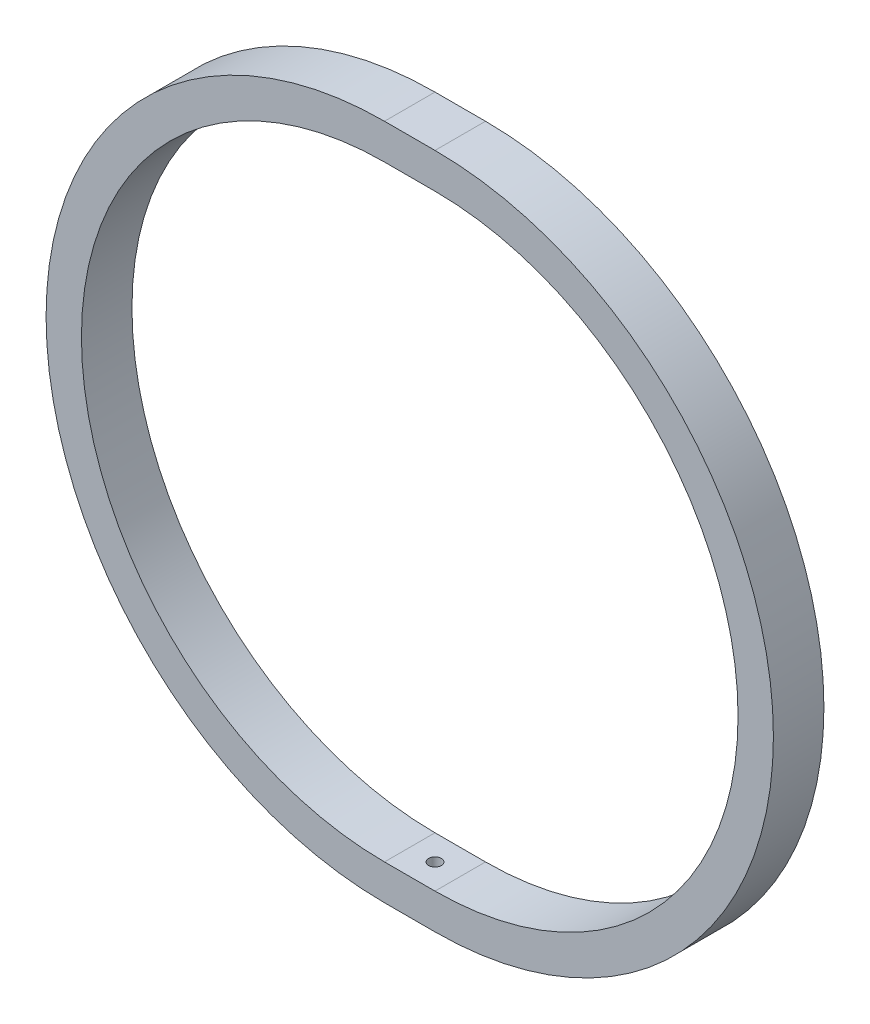
SolidWorks part; units mm, degrees
ref_plane "Front Plane" through (0, 0, 0) normal (0, 0, 1) x (1, 0, 0)
ref_plane "Top Plane" through (0, 0, 0) normal (0, 1, 0) x (1, 0, 0)
ref_plane "Right Plane" through (0, 0, 0) normal (1, 0, 0) x (0, 0, -1)
sketch "Sketch1" plane through (0, 0, 0) normal (1, 0, 0) x (0, 0, -1)
  line L0 (-29.8744, 0) -> (27.9622, 0) construction
  line L1 (-5, 67) -> (5, 67)
  line L2 (-5, 67) -> (-5, 60)
  line L3 (-5, 60) -> (5, 60)
  line L4 (5, 67) -> (5, 60)
  dimension "D1" = 7
  dimension "D2" = 10
  dimension "D3" = 5
  dimension "D4" = 60
revolve "Revolve1" add sketch "Sketch1" angle 180 about L0
sketch "Sketch2" plane through (0, 0, 0) normal (1, 0, 0) x (0, 0, -1)
  line L0 (-5, 67) -> (-5, 60) construction
  line L1 (-5, 60) -> (5, 60) construction
  line L2 (5, 60) -> (5, 67) construction
  line L3 (5, 67) -> (-5, 67) construction
  line L4 (-5, -60) -> (-5, -67) construction
  line L5 (-5, -67) -> (5, -67) construction
  line L6 (5, -67) -> (5, -60) construction
  line L7 (5, -60) -> (-5, -60) construction
  line L8 (-5, 67) -> (-5, 60)
  line L9 (-5, 60) -> (5, 60)
  line L10 (5, 60) -> (5, 67)
  line L11 (5, 67) -> (-5, 67)
  line L12 (-5, -60) -> (-5, -67)
  line L13 (-5, -67) -> (5, -67)
  line L14 (5, -67) -> (5, -60)
  line L15 (5, -60) -> (-5, -60)
extrude "Boss-Extrude1" add sketch "Sketch2" along normal blind 10
sketch "Sketch4" plane through (10, 0, 0) normal (1, 0, 0) x (0, 0, -1)
  line L0 (-23.3477, 0) -> (21.6309, 0) construction
  line L1 (35.75, 0) -> (-35.75, 0) construction
  line L6 (5, 67) -> (-5, 67)
  line L7 (-5, 67) -> (-5, 60)
  line L8 (-5, 60) -> (5, 60)
  line L9 (5, 60) -> (5, 67)
  line L10 (5, 67) -> (-5, 67)
  line L11 (-5, 67) -> (-5, 60)
  line L12 (-5, 60) -> (5, 60)
  line L13 (5, 60) -> (5, 67)
  dimension "D1" = 0
revolve "Revolve3" add sketch "Sketch4" angle 180 about L0
sketch "Sketch5" plane through (0, -60, 0) normal (0, 1, 0) x (1, 0, 0)
  line L0 (-79.2, 0) -> (79.2, 0) construction
  circle A0 centre (5, 0) radius 1.25
  dimension "D2" = 2.5
  dimension "D1" = 5
extrude "Cut-Extrude1" cut sketch "Sketch5" against normal blind 2.5
mirror "Mirror1" about plane through (0, 0, 0) normal (0, 1, 0) of "Cut-Extrude1"
